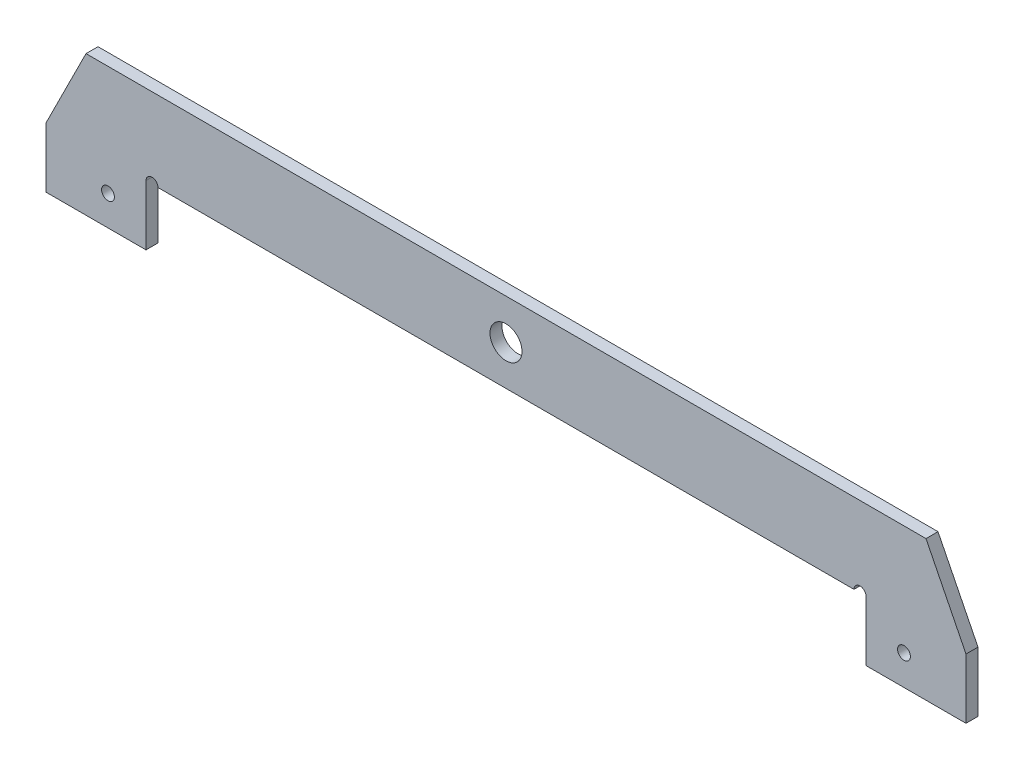
SolidWorks part; units mm, degrees
material "Thornel Mat VMA"
ref_plane "前视基准面" through (0, 0, 0) normal (0, 0, 1) x (1, 0, 0)
ref_plane "上视基准面" through (0, 0, 0) normal (0, 1, 0) x (1, 0, 0)
ref_plane "右视基准面" through (0, 0, 0) normal (1, 0, 0) x (0, 0, -1)
sketch "草图1" plane through (0, 0, 0) normal (0, 0, 1) x (1, 0, 0)
  line L0 (0, 72.9) -> (0, 0) construction
  line L1 (90, 0) -> (-90, 0)
  line L2 (-90, 0) -> (-90, -15)
  line L3 (-90, -15) -> (-115, -15)
  line L4 (-105, 0) -> (-105, 20)
  line L5 (-105, 20) -> (105, 20)
  line L6 (105, 0) -> (105, 20)
  line L7 (90, -15) -> (115, -15)
  line L8 (90, 0) -> (90, -15)
  line L9 (-105, 0) -> (-115, 0)
  line L10 (-115, 0) -> (-115, -15)
  line L11 (115, 0) -> (115, -15)
  line L12 (105, 0) -> (115, 0)
  circle A0 centre (0, 10) radius 4
  point P9 (0, 20)
  dimension "D6" = 8
  dimension "D7" = 10
  dimension "D1" = 180
  dimension "D2" = 15
  dimension "D3" = 25
  dimension "D4" = 15
  dimension "D5" = 10
extrude "凸台-拉伸1" add sketch "草图1" along normal blind 3
sketch "草图2" plane through (0, 0, 3) normal (0, 0, 1) x (1, 0, 0)
  line L0 (-90, 0) -> (90, 0) construction
  circle A0 centre (-88.5, 0) radius 1.5
  circle A1 centre (88.5, 0) radius 1.5
  dimension "D1" = 3
extrude "切除-拉伸1" cut sketch "草图2" against normal through all
sketch "草图3" plane through (0, 0, 3) normal (0, 0, 1) x (1, 0, 0)
  line L0 (-115, 0) -> (-105, 20)
  line L1 (-105, 20) -> (-105, 0)
  line L2 (-105, 0) -> (-115, 0)
  line L3 (105, 20) -> (105, 0)
  line L4 (105, 0) -> (115, 0)
  line L5 (115, 0) -> (105, 20)
extrude "凸台-拉伸2" add sketch "草图3" against normal up to surface (3 mm away) up to face at (0, -1.2143, 0)
sketch "草图4" plane through (0, 0, 3) normal (0, 0, 1) x (1, 0, 0)
  line L0 (-115, -7.5) -> (-99.5, -7.5) construction
  line L1 (-115, 0) -> (-115, -15) construction
  line L2 (-115, -15) -> (-90, -15) construction
  line L3 (0, 20) -> (0, -25.6241) construction
  line L4 (105, 20) -> (-105, 20) construction
  circle A0 centre (-99.5, -7.5) radius 1.6
  circle A1 centre (99.5, -7.5) radius 1.6
  dimension "D3" = 3.2
  dimension "D1" = 7.5
  dimension "D2" = 15.5
extrude "切除-拉伸2" cut sketch "草图4" against normal up to next
